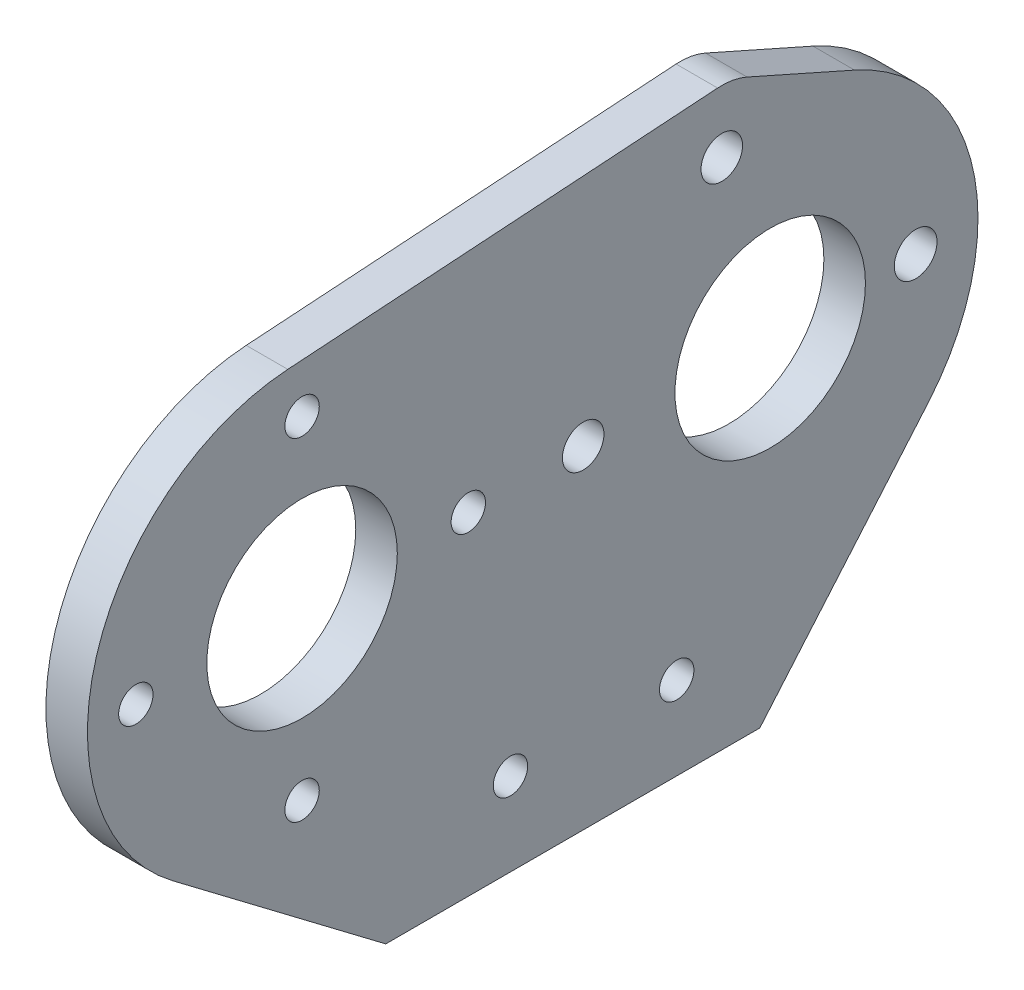
SolidWorks part; units mm, degrees
material "6061-T6 (SS)"
ref_plane "Front Plane" through (0, 0, 0) normal (0, 0, 1) x (1, 0, 0)
ref_plane "Top Plane" through (0, 0, 0) normal (0, 1, 0) x (1, 0, 0)
ref_plane "Right Plane" through (0, 0, 0) normal (1, 0, 0) x (0, 0, -1)
sketch "Sketch1" plane through (0, 0, 0) normal (1, 0, 0) x (0, 0, -1)
  line L0 (25.4, 12.7) -> (38.1, 12.7) construction
  line L1 (0, 0) -> (76.2, 0) construction
  line L5 (38.1, 12.7) -> (63.5, 12.7) construction
  line L6 (63.5, 12.7) -> (77.7875, 12.7) construction
  line L7 (77.7875, 12.7) -> (77.7875, 50.8) construction
  line L8 (77.7875, 50.8) -> (17.2031, 50.8) construction
  line L9 (76.2, 0) -> (101.9485, 30.2012)
  line L12 (6.2611, 50.8) -> (6.2611, 76.2) construction
  line L15 (38.1, 12.7) -> (38.1, 39.0177) construction
  line L18 (6.2611, 50.8) -> (6.2611, 25.4) construction
  line L19 (6.2611, 50.8) -> (31.6611, 50.8) construction
  line L20 (6.2611, 50.8) -> (-19.1389, 50.8) construction
  line L22 (77.7875, 50.8) -> (6.2611, 50.8) construction
  line L23 (0, 0) -> (19.05, 0) construction
  line L24 (19.05, 0) -> (-13.5263, 24.6517)
  line L25 (19.05, 0) -> (76.2, 0)
  line L26 (77.7875, 50.8) -> (70.3917, 78.4013) construction
  line L27 (90.6722, 79.818) -> (74.2572, 87.1067)
  line L28 (69.757, 87.9052) -> (4.0759, 83.5185)
  line L29 (77.7875, 50.8) -> (100.0125, 50.8) construction
  circle A0 centre (38.1, 12.7) radius 2.6289
  circle A1 centre (63.5, 12.7) radius 2.6289
  circle A2 centre (77.7875, 50.8) radius 14.5542
  arc A3 (101.9485, 30.2012) -> (90.6722, 79.818) centre (77.7875, 50.8) ccw
  circle A4 centre (6.2611, 50.8) radius 14.5542
  circle A5 centre (6.2611, 76.2) radius 2.6289
  arc A9 (4.0759, 83.5185) -> (-13.5263, 24.6517) centre (6.2611, 50.8) ccw
  circle A10 centre (6.2611, 25.4) radius 2.6289
  circle A11 centre (31.6611, 50.8) radius 2.6289
  circle A12 centre (-19.1389, 50.8) radius 2.6289
  circle A13 centre (49.2125, 50.8) radius 3.175
  circle A14 centre (70.3917, 78.4013) radius 3.175
  arc A15 (69.757, 87.9052) -> (74.2572, 87.1067) centre (70.3917, 78.4013) cw
  circle A16 centre (100.0125, 50.8) radius 3.2639
  dimension "D5" = 5.2578
  dimension "D6" = 5.2578
  dimension "D9" = 29.1084
  dimension "D10" = 63.5
  dimension "D11" = 29.1084
  dimension "D13" = 5.2578
  dimension "D15" = 65.5828
  dimension "D17" = 5.2578
  dimension "D19" = 5.2578
  dimension "D21" = 5.2578
  dimension "D24" = 19.05
  dimension "D25" = 28.575
  dimension "D26" = 6.35
  dimension "D28" = 28.575
  dimension "D29" = 6.35
  dimension "D30" = 9.525
  dimension "D31" = 22.225
  dimension "D32" = 6.5278
  dimension "D2" = 76.2
  dimension "D3" = 12.7
  dimension "D4" = 25.4
  dimension "D7" = 14.2875
  dimension "D8" = 38.1
  dimension "D12" = 25.4
  dimension "D16" = 71.5264
  dimension "D14" = 25.4
  dimension "D18" = 25.4
  dimension "D20" = 25.4
  dimension "D22" = 12.7
  dimension "D23" = 12.7
  dimension "D27" = 75
extrude "Core geometry" add sketch "Sketch1" along normal blind 6.35
